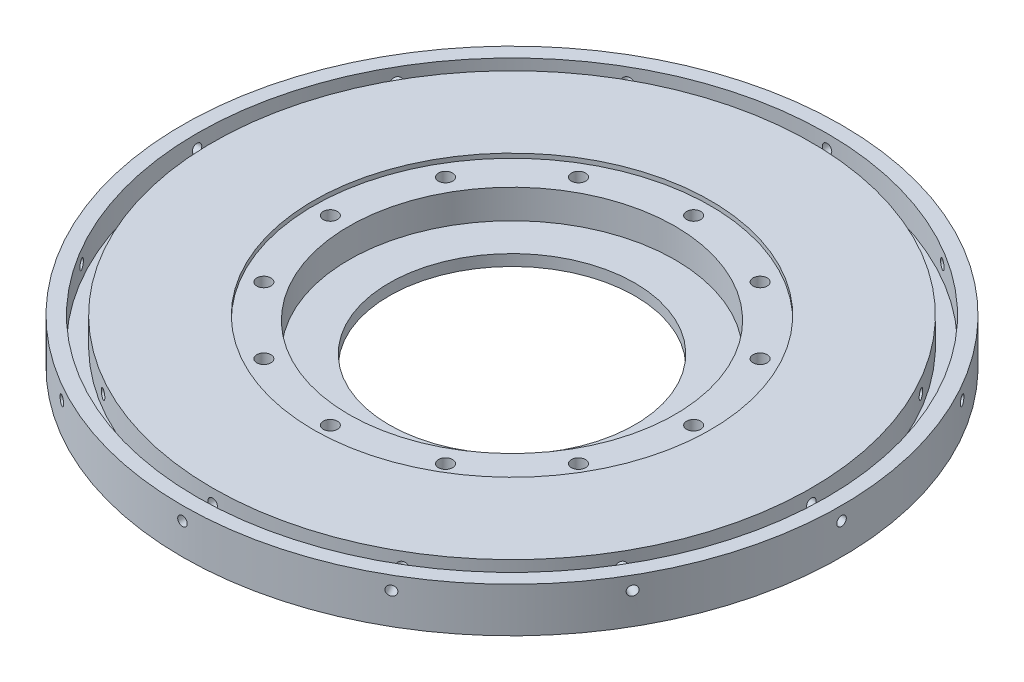
SolidWorks part; units mm, degrees
material "6061-T6 (SS)"
ref_plane "Front Plane" through (0, 0, 0) normal (0, 0, 1) x (1, 0, 0)
ref_plane "Top Plane" through (0, 0, 0) normal (0, 1, 0) x (1, 0, 0)
ref_plane "Right Plane" through (0, 0, 0) normal (1, 0, 0) x (0, 0, -1)
sketch "Sketch1" plane through (0, 0, 0) normal (0, 1, 0) x (1, 0, 0)
  line L5 (0, 0) -> (127.635, 0)
  line L6 (0, 0) -> (0, 127.635)
  line L7 (0, 127.635) -> (127.635, 127.635)
  line L8 (127.635, 0) -> (127.635, 127.635)
  dimension "D1" = 127.635
  dimension "D2" = 127.635
extrude "Boss-Extrude1" add sketch "Sketch1" along normal blind 9.525 contours L5 L8 L7 L6
sketch "Sketch13" plane through (0, 9.525, 0) normal (0, 1, 0) x (1, 0, 0)
  circle A0 centre (63.8175, 63.8175) radius 93.6625
  dimension "D1" = 187.325
extrude "Boss-Extrude2" add sketch "Sketch13" against normal blind 12.7 contours A0
sketch "Sketch6" [suppressed] plane through (127.635, 0, 0) normal (1, 0, 0) x (0, 0, -1)
  circle A0 centre (4.7625, 4.7625) radius 1.3526
  dimension "D1" = 2.7051
extrude "6-32 hole1" [suppressed] cut sketch "Sketch6" against normal blind 12.7
sketch "Sketch7" [suppressed] plane through (0, 0, -127.635) normal (0, 0, -1) x (-1, 0, 0)
  circle A0 centre (-122.8725, 4.7625) radius 1.3525
  dimension "D1" = 2.7051
sketch "Sketch8" [suppressed] plane through (0, 0, 0) normal (-1, 0, 0) x (0, 0, 1)
  circle A0 centre (-122.8725, 4.7625) radius 1.3525
  dimension "D1" = 2.7051
sketch "Sketch9" [suppressed] plane through (0, 0, 0) normal (0, 0, 1) x (1, 0, 0)
  circle A0 centre (4.7625, 4.7625) radius 1.3526
  dimension "D1" = 2.7051
sketch "Sketch5" plane through (0, 9.525, 0) normal (0, 1, 0) x (1, 0, 0)
  circle A0 centre (63.8175, 63.8175) radius 46.355
  circle A1 centre (63.8175, 63.8175) radius 93.6625 construction
  dimension "D1" = 92.71
extrude "Cut-Extrude1" cut sketch "Sketch5" against normal blind 9.525
sketch "Sketch11" plane through (0, 9.525, 0) normal (0, 1, 0) x (1, 0, 0)
  line L0 (63.8175, 63.8175) -> (63.8175, 115.443) construction
  circle A0 centre (63.8175, 115.443) radius 2.0193
  dimension "D2" = 4.0386
  dimension "D1" = 51.6255
extrude "Cut-Extrude3" cut sketch "Sketch11" against normal through all contours A0
pattern_circular "CirPattern1" count 12 over 360 about axis through (63.8175, 0, -63.8175) along (0, 1, 0) of "Cut-Extrude3"
sketch "Sketch12" plane through (0, 9.525, 0) normal (0, 1, 0) x (1, 0, 0)
  circle A0 centre (63.8175, 63.8175) radius 56.4198
  dimension "D1" = 112.8395
extrude "Cut-Extrude4" cut sketch "Sketch12" against normal blind 1.27
sketch "Sketch15" plane through (0, 9.525, 0) normal (0, 1, 0) x (1, 0, 0)
  line L0 (63.8175, 63.8175) -> (-29.845, 63.8175) construction
  line L1 (0, -39.1057) -> (0, 39.1057) construction
  line L2 (-20.0025, 63.8175) -> (-25.0825, 63.8175)
  line L3 (-8.7458, 105.7742) -> (-13.2051, 108.2104)
  line L4 (-8.7458, 105.7742) -> (-20.0025, 63.8175) construction
  circle A0 centre (63.8175, 63.8175) radius 56.4198 construction
  arc A1 (-20.0025, 63.8175) -> (-8.7458, 105.7742) centre (63.8175, 63.8175) cw
  arc A2 (-25.0825, 63.8175) -> (-13.2051, 108.2104) centre (63.8175, 63.8175) cw
  circle A3 centre (63.8175, 63.8175) radius 93.6625 construction
  point P0 (63.8175, 63.8175)
  point P11 (-14.3741, 84.7959)
  dimension "D1" = 46.482
  dimension "D2" = 88.9
  dimension "D3" = 83.82
  dimension "D4" = 43.942
sketch "Sketch16" plane through (0, 9.525, 0) normal (0, 1, 0) x (1, 0, 0)
  circle A0 centre (63.8175, 63.8175) radius 89.535
  circle A1 centre (63.8175, 63.8175) radius 85.09
  dimension "D1" = 179.07
  dimension "D2" = 170.18
extrude "Cut-Extrude5" cut sketch "Sketch16" against normal blind 7.62
sketch "Sketch18" plane through (0, 8.255, 0) normal (0, 1, 0) x (1, 0, 0)
  line L0 (63.8175, 185.7252) -> (63.8175, -48.6103) construction
ref_plane "Plane1" through (63.8175, 0, 0) normal (-1, 0, 0) x (0, 0, 1)
ref_plane "Plane2" through (0, 0, 29.845) normal (0, 0, 1) x (1, 0, 0)
sketch "Sketch17" plane through (0, 0, 29.845) normal (0, 0, 1) x (1, 0, 0)
  line L0 (63.8175, 103.0287) -> (63.8175, -103.0287) construction
  line L1 (157.48, 9.525) -> (-29.845, 9.525) construction
  circle A0 centre (63.8175, 5.715) radius 1.3525
  dimension "D1" = 2.7051
  dimension "D2" = 3.81
extrude "Cut-Extrude6" cut sketch "Sketch17" against normal blind 15.24
pattern_circular "CirPattern2" count 12 over 360 about axis through (63.8175, 0, -63.8175) along (0, 1, 0) of "Cut-Extrude6"
sketch "Sketch19" plane through (0, -3.175, 0) normal (0, -1, 0) x (1, 0, 0)
  circle A0 centre (63.8175, -63.8175) radius 34.925
  dimension "D1" = 69.85
extrude "Cut-Extrude7" cut sketch "Sketch19" against normal blind 87.63
